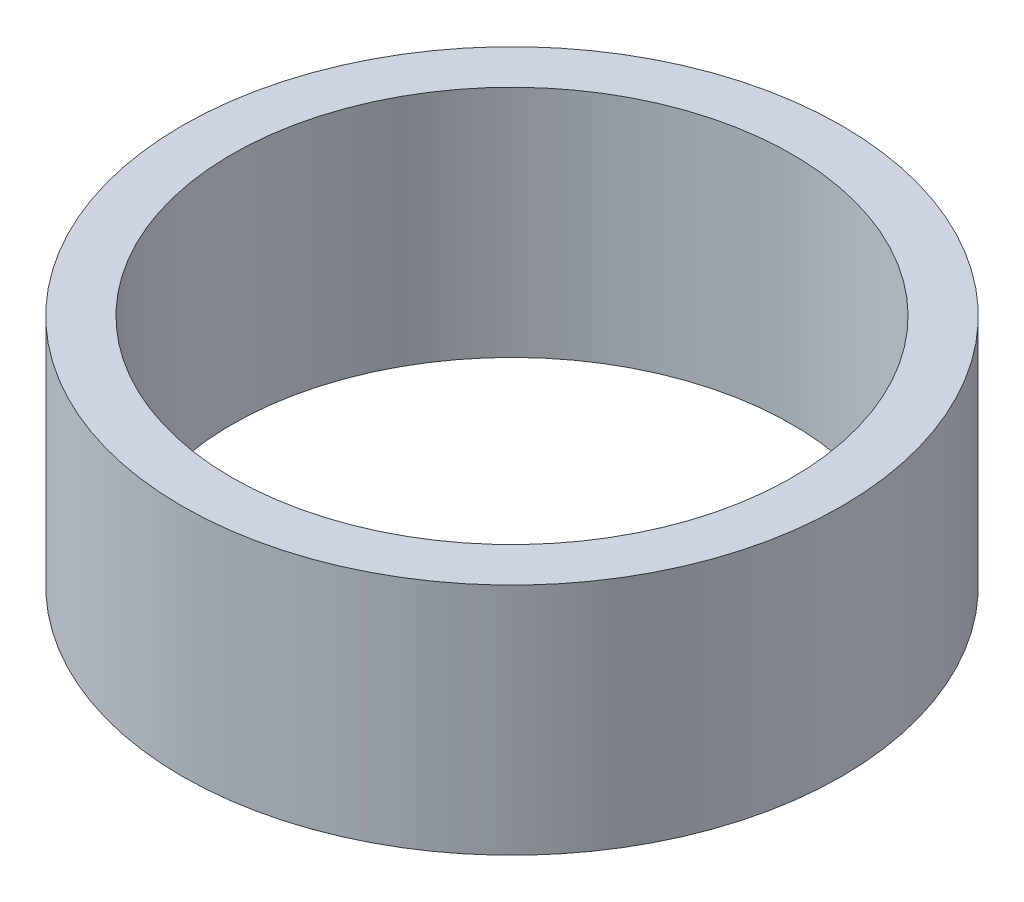
SolidWorks part; units mm, degrees
ref_plane "Front Plane" through (0, 0, 0) normal (0, 0, 1) x (1, 0, 0)
ref_plane "Top Plane" through (0, 0, 0) normal (0, 1, 0) x (1, 0, 0)
ref_plane "Right Plane" through (0, 0, 0) normal (1, 0, 0) x (0, 0, -1)
sketch "Sketch1" plane through (0, 0, 0) normal (0, 1, 0) x (1, 0, 0)
  circle A0 centre (0, 0) radius 23.25
extrude "Boss-Extrude1" add sketch "Sketch1" along normal blind 16.5
sketch "Sketch2" plane through (0, 16.5, 0) normal (0, 1, 0) x (1, 0, 0)
  circle A0 centre (0, 0) radius 19.75
  point P2 (6.6793, -4.3772)
  point P3 (0, 0)
extrude "Cut-Extrude1" cut sketch "Sketch2" against normal blind 16.5 contours A0
